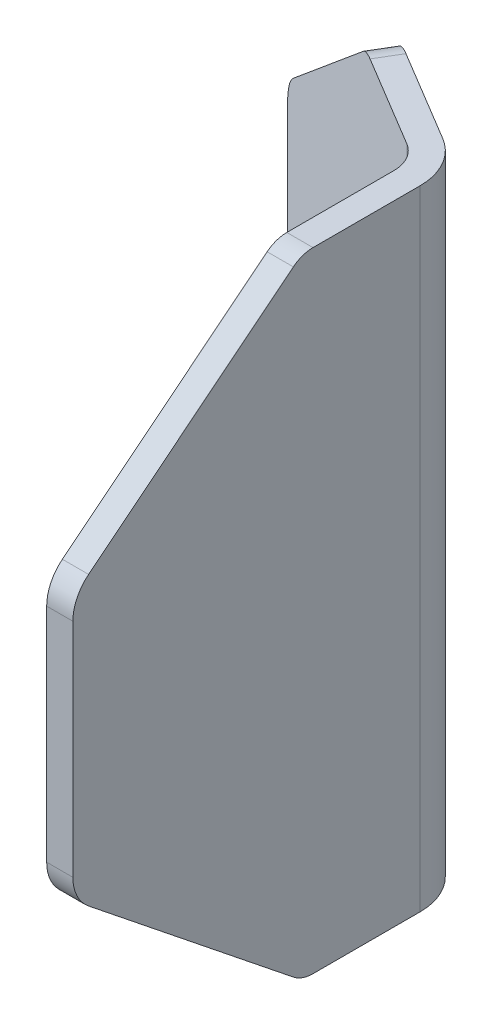
SolidWorks part; units mm, degrees
material "6061-T6 (SS)"
ref_plane "Front Plane" through (0, 0, 0) normal (0, 0, 1) x (1, 0, 0)
ref_plane "Top Plane" through (0, 0, 0) normal (0, 1, 0) x (1, 0, 0)
ref_plane "Right Plane" through (0, 0, 0) normal (1, 0, 0) x (0, 0, -1)
sketch "Sketch1" plane through (0, 0, 0) normal (0, 1, 0) x (1, 0, 0)
  line L0 (-39.6682, 23.7869) -> (-3.5779, 2.1455)
  line L1 (0, -46.2534) -> (0, -4.1718)
  line L2 (-41.301, 21.0639) -> (-5.2107, -0.5775)
  line L3 (-3.175, -46.2534) -> (-3.175, -4.1718)
  line L4 (-39.6682, 23.7869) -> (-41.301, 21.0639)
  line L5 (-3.175, -46.2534) -> (0, -46.2534)
  arc A0 (-5.2107, -0.5775) -> (-3.175, -4.1718) centre (-7.366, -4.1718) cw
  arc A1 (-3.5779, 2.1455) -> (0, -4.1718) centre (-7.366, -4.1718) cw
  dimension "D5" = 4.191
  dimension "D1" = 3.175
  dimension "D2" = 42.0816
  dimension "D3" = 42.0816
  dimension "D4" = 120.949
  dimension "D6" = 4.1718
extrude "Boss-Extrude2" add sketch "Sketch1" along normal blind 76.2
sketch "Sketch2" plane through (0, 0, 0) normal (1, 0, 0) x (0, 0, -1)
  line L0 (-46.2534, 53.975) -> (-18.4944, 76.2)
  line L1 (-46.2534, 76.2) -> (-46.2534, 0) construction
  line L2 (-46.2534, 76.2) -> (-4.1718, 76.2) construction
  line L3 (-46.2534, 22.225) -> (-46.2534, 0)
  line L4 (-46.2534, 22.225) -> (-18.4944, 0)
  line L5 (-46.2534, 0) -> (-4.1718, 0) construction
  line L6 (-46.2534, 0) -> (-18.4944, 0)
  line L7 (-46.2534, 53.975) -> (-46.2534, 76.2)
  line L9 (-46.2534, 76.2) -> (-18.4944, 76.2)
  dimension "D1" = 35.56
  dimension "D2" = 35.56
  dimension "D3" = 31.75
extrude "Cut-Extrude3" cut sketch "Sketch2" against normal up to next contours L4 L6 L3 | L0 L9 L7
sketch "Sketch4" plane through (0, 0, 0) normal (0.5143, 0, -0.8576) x (-0.8576, 0, -0.5143)
  line L0 (46.2534, 22.225) -> (46.2534, 53.975) construction
  line L1 (46.2534, 76.2) -> (46.2534, 0) construction
  line L2 (4.1718, 76.2) -> (4.1718, 0) construction
  line L3 (46.2534, 53.975) -> (18.4944, 76.2)
  line L4 (4.1718, 76.2) -> (46.2534, 76.2) construction
  line L5 (18.4944, 0) -> (46.2534, 22.225)
  line L6 (4.1718, 0) -> (46.2534, 0) construction
  line L7 (18.4944, 76.2) -> (46.2534, 76.2)
  line L8 (46.2534, 76.2) -> (46.2534, 53.975)
  line L9 (18.4944, 0) -> (46.2534, 0)
  line L10 (46.2534, 0) -> (46.2534, 22.225)
  point P4 (46.2534, 38.1)
  point P7 (4.1718, 38.1)
  dimension "D1" = 31.75
  dimension "D2" = 35.56
  dimension "D3" = 35.56
extrude "Cut-Extrude4" cut sketch "Sketch4" against normal up to next
fillet "Fillet1" radius 5.08 4 edges at (-40.4846, 22.225, -22.4254) (-40.4846, 53.975, -22.4254) (-1.5875, 22.225, 46.2534) (-1.5875, 53.975, 46.2534)
fillet "Fillet2" radius 3.81 4 edges at (-1.5875, 0, 18.4944) (-16.6777, 0, -8.1497) (-1.5875, 76.2, 18.4944) (-16.6777, 76.2, -8.1497)
